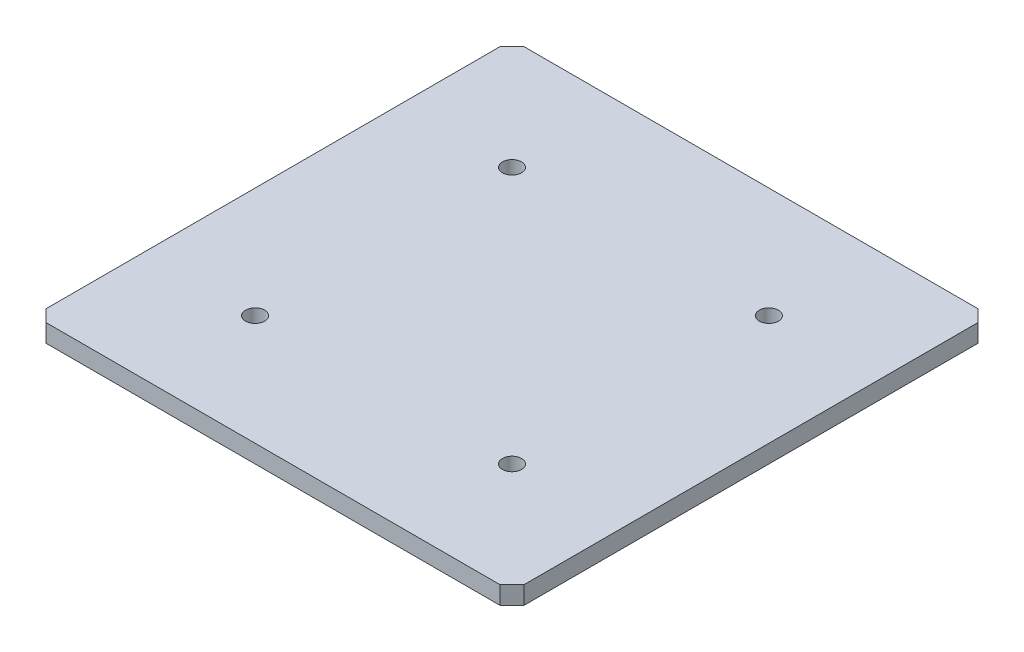
SolidWorks part; units mm, degrees
material "PLA"
ref_plane "Front Plane" through (0, 0, 0) normal (0, 0, 1) x (1, 0, 0)
ref_plane "Top Plane" through (0, 0, 0) normal (0, 1, 0) x (1, 0, 0)
ref_plane "Right Plane" through (0, 0, 0) normal (1, 0, 0) x (0, 0, -1)
sketch "Sketch1" plane through (0, 0, 0) normal (0, 1, 0) x (1, 0, 0)
  line L1 (0, 0) -> (400, 0)
  line L2 (0, 0) -> (0, 400)
  line L3 (0, 400) -> (400, 400)
  line L4 (400, 0) -> (400, 400)
  dimension "D1" = 400
  dimension "D2" = 400
extrude "Boss-Extrude1" add sketch "Sketch1" along normal mid plane 15
chamfer "Chamfer1" distance 10 angle 45 4 edges at (0, 0, -400) (400, 0, -400) (0, 0, 0) (400, 0, 0)
sketch "Sketch3" plane through (0, 7.5, 0) normal (0, 1, 0) x (1, 0, 0)
  line L0 (400, 10) -> (400, 390) construction
  line L1 (92.5, 92.5) -> (307.5, 92.5) construction
  line L2 (92.5, 92.5) -> (92.5, 307.5) construction
  line L3 (92.5, 307.5) -> (307.5, 307.5) construction
  line L4 (307.5, 92.5) -> (307.5, 307.5) construction
  line L5 (92.5, 92.5) -> (307.5, 307.5) construction
  line L6 (92.5, 307.5) -> (307.5, 92.5) construction
  line L7 (10, 0) -> (390, 0) construction
  circle A4 centre (307.5, 307.5) radius 8
  circle A5 centre (307.5, 92.5) radius 8
  circle A6 centre (92.5, 92.5) radius 8
  circle A7 centre (92.5, 307.5) radius 8
  point P0 (200, 200)
  point P12 (400, 200)
  point P16 (200, 0)
  point P25 (200, 200)
  dimension "D1" = 215
  dimension "D3" = 16
  dimension "D2" = 215
  dimension "D4" = 4
extrude "Cut-Extrude1" cut sketch "Sketch3" against normal blind 16
